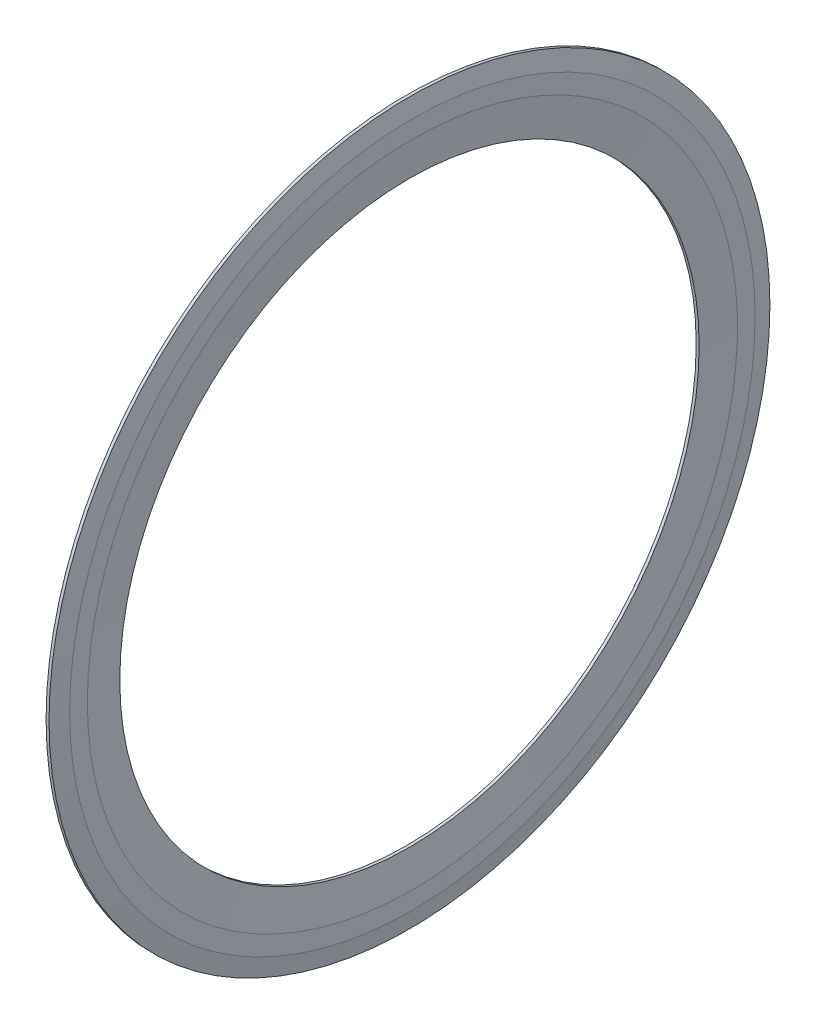
SolidWorks part; units mm, degrees
material "普通碳钢"
ref_plane "前视基准面" through (0, 0, 0) normal (0, 0, 1) x (1, 0, 0)
ref_plane "上视基准面" through (0, 0, 0) normal (0, 1, 0) x (1, 0, 0)
ref_plane "右视基准面" through (0, 0, 0) normal (1, 0, 0) x (0, 0, -1)
ref_plane "基准面1" through (0, 0, 0) normal (0, 0, 1) x (1, 0, 0)
sketch "草图1" plane through (0, 0, 0) normal (0, 0, 1) x (1, 0, 0)
  line L0 (0.27, 11.075) -> (0.315, 10.5312)
  line L1 (0.315, 10.5312) -> (0.27, 9.9875)
  line L2 (0.27, 9.9875) -> (0.27, 8.9)
  line L3 (0.27, 8.9) -> (0.36, 8.9)
  line L4 (0.36, 8.9) -> (0.45, 9.9875)
  line L5 (0.45, 9.9875) -> (0.45, 10.5312)
  line L6 (0.45, 10.5312) -> (0.36, 11.075)
  line L7 (0.36, 11.075) -> (0.27, 11.075)
  line L8 (50, 0) -> (-50, 0) construction
revolve "旋转1" add sketch "草图1" angle 360 about L8
